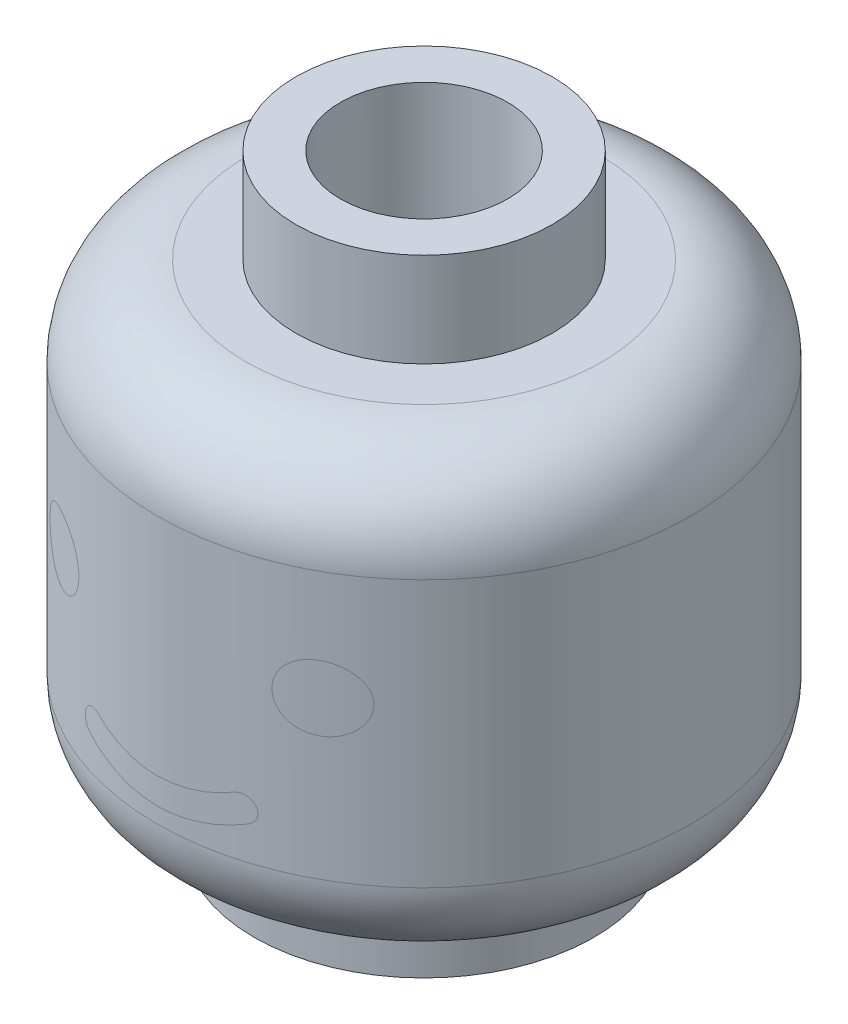
SolidWorks part; units mm, degrees
ref_plane "Front Plane" through (0, 0, 0) normal (0, 0, 1) x (1, 0, 0)
ref_plane "Top Plane" through (0, 0, 0) normal (0, 1, 0) x (1, 0, 0)
ref_plane "Right Plane" through (0, 0, 0) normal (1, 0, 0) x (0, 0, -1)
sketch "Sketch1" plane through (0, 0, 0) normal (1, 0, 0) x (0, 0, -1)
  line L0 (0, 16.3137) -> (0, 0) construction
  line L1 (0, 8.5) -> (0, 9.4)
  line L2 (0, 9.4) -> (1.6, 9.4)
  line L3 (1.6, 9.4) -> (1.6, 11.4)
  line L4 (1.6, 11.4) -> (2.45, 11.4)
  line L5 (2.45, 11.4) -> (2.45, 9.6)
  line L6 (2.45, 9.6) -> (3.4, 9.6)
  line L7 (5.1, 7.9) -> (5.1, 2.8)
  line L8 (3.4, 1.1) -> (3.25, 1.1)
  line L9 (3.25, 1.1) -> (3.25, 0)
  line L10 (3.25, 0) -> (2.45, 0)
  line L11 (2.45, 0) -> (2.45, 8.5)
  line L12 (2.45, 8.5) -> (0, 8.5)
  arc A0 (5.1, 2.8) -> (3.4, 1.1) centre (3.4, 2.8) cw
  arc A1 (3.4, 9.6) -> (5.1, 7.9) centre (3.4, 7.9) cw
  point P17 (5.1, 1.1)
  point P20 (5.1, 9.6)
  dimension "D10" = 1.7
  dimension "D1" = 9.6
  dimension "D2" = 1.1
  dimension "D3" = 0.8
  dimension "D4" = 2.9
  dimension "D5" = 2
  dimension "D6" = 1.8
  dimension "D7" = 4.9
  dimension "D8" = 3.2
  dimension "D9" = 2.65
revolve "Head Revolve" add sketch "Sketch1" angle 360 about L0
sketch "Sketch2" plane through (0, 9.4, 0) normal (0, 1, 0) x (1, 0, 0)
  line L0 (0, 1.6) -> (0, 0) construction
  line L1 (0, 0) -> (-1.3856, -0.8) construction
  line L2 (-0.42, 1.5439) -> (-0.42, 0.2425)
  line L3 (-0.42, 0.2425) -> (-1.547, -0.4082)
  line L4 (-0.42, 1.6) -> (-0.42, 0.2425) construction
  line L5 (-0.42, 0.2425) -> (-1.5956, -0.4363) construction
  circle A0 centre (0, 0) radius 1.6 construction
  circle A1 centre (0, 0) radius 1.6 construction
  arc A2 (-0.42, 1.5439) -> (-1.547, -0.4082) centre (0, 0) ccw
  dimension "D1" = 120
  dimension "D2" = 0.42
extrude "Air Hole" cut sketch "Sketch2" against normal blind 10
pattern_circular "CircPattern" count 3 over 360 about axis through (0, 0, 0) along (0, 1, 0) of "Air Hole"
sketch "Sketch3" plane through (0, 0, 0) normal (0, 0, 1) x (1, 0, 0)
  line L0 (0, 11.4) -> (0, 0) construction
  line L3 (2.45, 11.4) -> (-2.45, 11.4) construction
  line L4 (-5.1, 5.8) -> (5.1, 5.8) construction
  line L5 (-5.1, 7.9) -> (-5.1, 2.8) construction
  line L6 (5.1, 2.8) -> (5.1, 7.9) construction
  line L7 (-5.1, 3.1) -> (5.1, 3.1) construction
  line L8 (-3.25, 0) -> (3.25, 0) construction
  circle A0 centre (-2.47, 5.8) radius 0.625
  circle A1 centre (2.47, 5.8) radius 0.625
  arc A2 (-1.4, 3.667) -> (1.4, 3.667) centre (0, 6.6) ccw construction
  arc A3 (-1.5077, 3.4414) -> (1.5077, 3.4414) centre (0, 6.6) ccw
  arc A4 (-1.2923, 3.8926) -> (1.2923, 3.8926) centre (0, 6.6) ccw
  arc A5 (-1.2923, 3.8926) -> (-1.5077, 3.4414) centre (-1.4, 3.667) ccw
  arc A6 (1.5077, 3.4414) -> (1.2923, 3.8926) centre (1.4, 3.667) ccw
  point P21 (0, 3.35)
  dimension "D3" = 1.25
  dimension "D4" = 4.94
  dimension "D5" = 0.25
  dimension "D7" = 3.5
  dimension "D1" = 3.1
  dimension "D2" = 5.6
  dimension "D6" = 2.8
split line "Split Line1"
